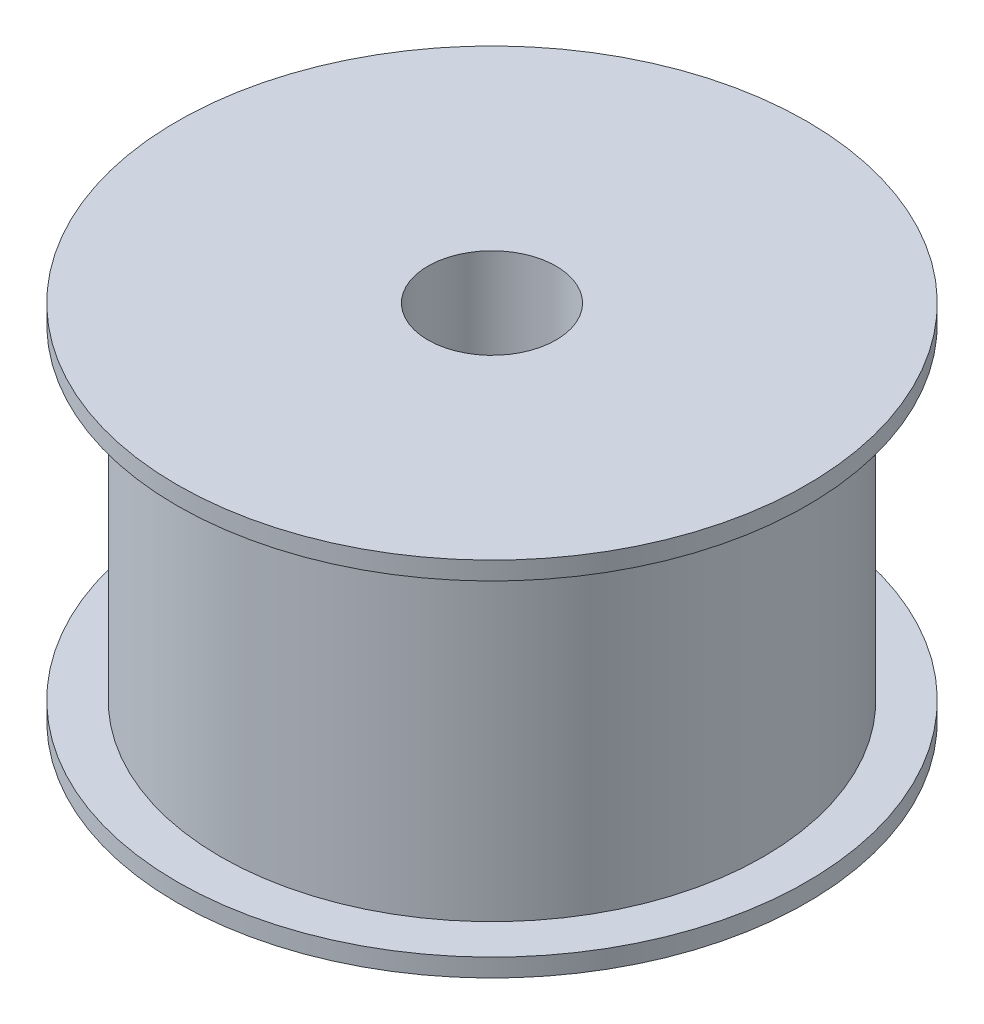
SolidWorks part; units mm, degrees
ref_plane "Front Plane" through (0, 0, 0) normal (0, 0, 1) x (1, 0, 0)
ref_plane "Top Plane" through (0, 0, 0) normal (0, 1, 0) x (1, 0, 0)
ref_plane "Right Plane" through (0, 0, 0) normal (1, 0, 0) x (0, 0, -1)
sketch "Sketch1" plane through (0, 0, 0) normal (0, 0, 1) x (1, 0, 0)
  line L0 (0, 0) -> (0, 12.7)
  line L1 (0, 12.7) -> (11.049, 12.7)
  line L2 (11.049, 12.7) -> (11.049, 12.065)
  line L3 (11.049, 12.065) -> (9.525, 12.065)
  line L4 (9.525, 12.065) -> (9.525, 0.635)
  line L5 (9.525, 0.635) -> (11.049, 0.635)
  line L6 (11.049, 0.635) -> (11.049, 0)
  line L7 (11.049, 0) -> (0, 0)
  dimension "D1" = 1.524
  dimension "D2" = 0.635
  dimension "D3" = 9.525
  dimension "D4" = 12.7
revolve "Revolve1" add sketch "Sketch1" angle 360 about L0
hole_wizard "#8 Clearance Hole1" positions "Sketch3" profile "Sketch4" hole size "#8" standard "ANSI Inch" end condition through all
sketch "Sketch3" plane through (0, 12.7, 0) normal (0, 1, 0) x (1, 0, 0)
  point P0 (0, 0)
sketch "Sketch4" plane through (0, 12.7, 0) normal (1, 0, 0) x (0, 0, 1)
  line L0 (0, 0) -> (0, 12.7)
  line L1 (0, 12.7) -> (2.2479, 12.7)
  line L2 (2.2479, 12.7) -> (2.2479, 0)
  line L5 (2.2479, 0) -> (0, 0)
  line L11 (0, -6.35) -> (0, 107.95) construction
  dimension "Thru Hole Dia." = 4.4958
  dimension "Thru Hole Depth" = 12.7
